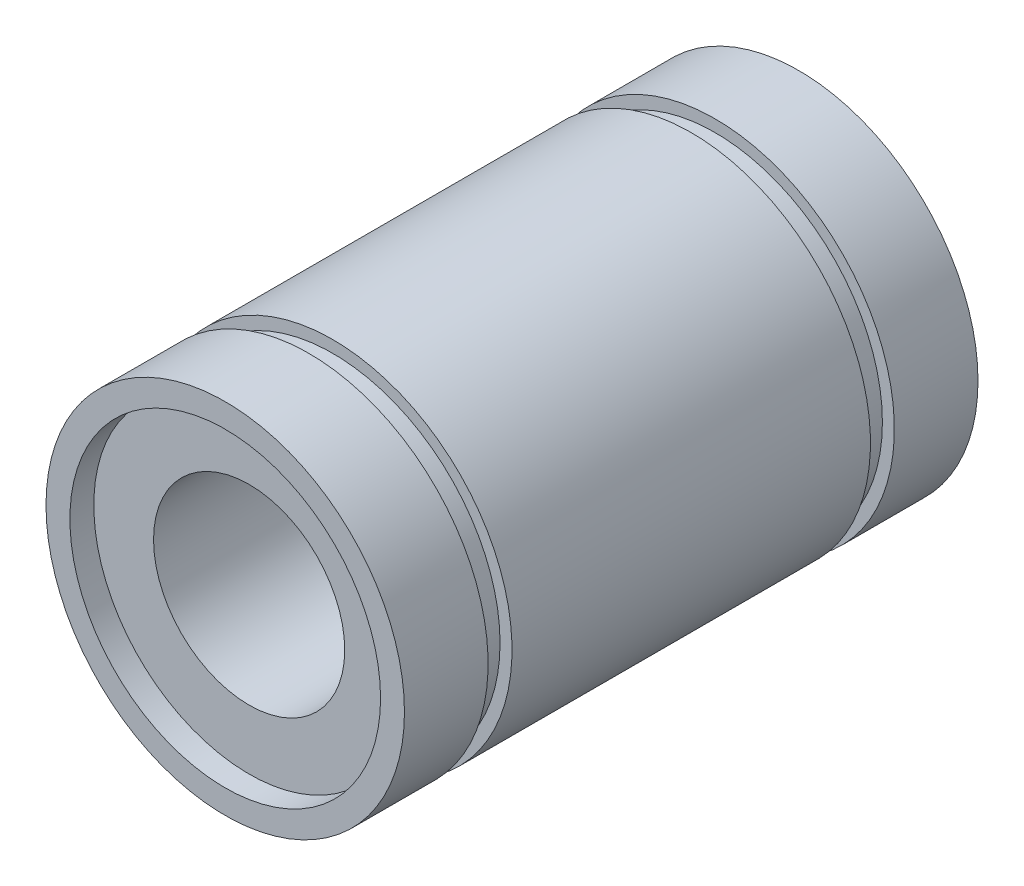
SolidWorks part; units mm, degrees
ref_plane "Front Plane" through (0, 0, 0) normal (0, 0, 1) x (1, 0, 0)
ref_plane "Top Plane" through (0, 0, 0) normal (0, 1, 0) x (1, 0, 0)
ref_plane "Right Plane" through (0, 0, 0) normal (1, 0, 0) x (0, 0, -1)
sketch "Sketch1" plane through (0, 0, 0) normal (0, 0, 1) x (1, 0, 0)
  circle A0 centre (0, 0) radius 7.5
  circle A1 centre (0, 0) radius 6.5
  dimension "D1" = 15
  dimension "D2" = 1
extrude "Boss-Extrude1" add sketch "Sketch1" along normal mid plane 24
sketch "Sketch2" plane through (0, 0, 0) normal (0, 0, 1) x (1, 0, 0)
  circle A1 centre (0, 0) radius 4
  circle A2 centre (0, 0) radius 6.5
  circle A3 centre (0, 0) radius 6.5
  dimension "D2" = 8
  dimension "D1" = 0
extrude "Boss-Extrude2" add sketch "Sketch2" along normal mid plane 22 separate body
sketch "Sketch3" plane through (0, 0, 0) normal (0, 1, 0) x (1, 0, 0)
  line L0 (7.5, -12) -> (7.5, 12) construction
  line L1 (7.5, 8.5) -> (7, 8.5)
  line L2 (7.5, 8.5) -> (7.5, 7.5)
  line L3 (7.5, 7.5) -> (7, 7.5)
  line L4 (7, 8.5) -> (7, 7.5)
  line L5 (-7.5, 0) -> (7.5, 0) construction
  line L6 (-7.5, 12) -> (-7.5, -12) construction
  line L7 (7.5, -8.5) -> (7.5, -7.5)
  line L8 (7.5, -7.5) -> (7, -7.5)
  line L9 (7, -8.5) -> (7, -7.5)
  line L10 (7.5, -8.5) -> (7, -8.5)
  line L11 (0, 12) -> (0, -12) construction
  line L12 (7.5, 12) -> (-7.5, 12) construction
  line L13 (-7.5, -12) -> (7.5, -12) construction
  dimension "D1" = 1
  dimension "D2" = 15
  dimension "D3" = 0.5
revolve "Cut-Revolve1" cut sketch "Sketch3" angle 360 about L11
